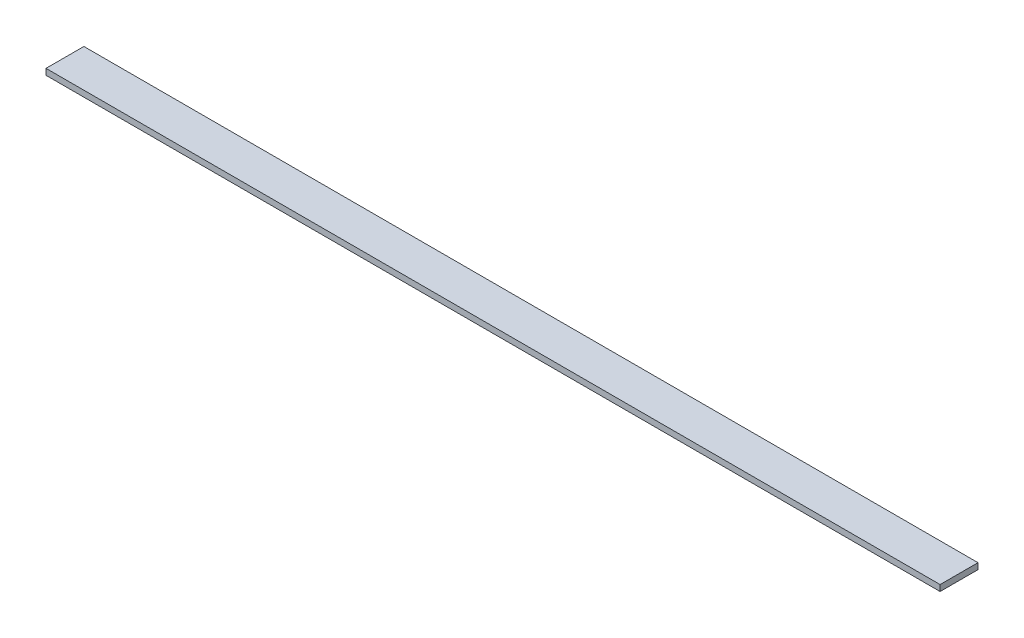
SolidWorks part; units mm, degrees
ref_plane "Спереди" through (0, 0, 0) normal (0, 0, 1) x (1, 0, 0)
ref_plane "Сверху" through (0, 0, 0) normal (0, 1, 0) x (1, 0, 0)
ref_plane "Справа" through (0, 0, 0) normal (1, 0, 0) x (0, 0, -1)
sketch "Эскиз1" plane through (0, 0, 0) normal (0, 1, 0) x (1, 0, 0)
  line L1 (-590, 25) -> (590, 25)
  line L2 (-590, 25) -> (-590, -25)
  line L3 (-590, -25) -> (590, -25)
  line L4 (590, 25) -> (590, -25)
  line L5 (-590, 25) -> (590, -25) construction
  line L6 (-590, -25) -> (590, 25) construction
  point P0 (0, 0)
extrude "Бобышка-Вытянуть1" add sketch "Эскиз1" along normal blind 8
